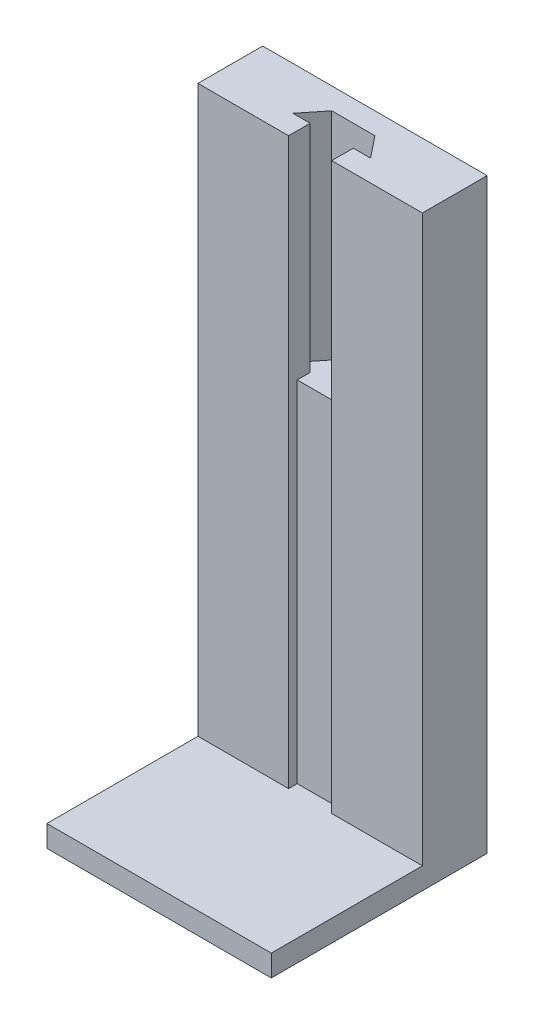
SolidWorks part; units mm, degrees
ref_plane "Front Plane" through (0, 0, 0) normal (0, 0, 1) x (1, 0, 0)
ref_plane "Top Plane" through (0, 0, 0) normal (0, 1, 0) x (1, 0, 0)
ref_plane "Right Plane" through (0, 0, 0) normal (1, 0, 0) x (0, 0, -1)
sketch "Sketch1" plane through (0, 0, 0) normal (0, 1, 0) x (1, 0, 0)
  line L1 (-26, -25) -> (26, -25)
  line L2 (-26, -25) -> (-26, 25)
  line L3 (-26, 25) -> (26, 25)
  line L4 (26, -25) -> (26, 25)
  line L5 (-26, -25) -> (26, 25) construction
  line L6 (-26, 25) -> (26, -25) construction
  point P0 (0, 0)
  dimension "D1" = 50
  dimension "D2" = 52
extrude "Boss-Extrude1" add sketch "Sketch1" along normal blind 5
sketch "Sketch2" plane through (0, 5, 0) normal (0, 1, 0) x (1, 0, 0)
  line L0 (26, -25) -> (26, 25) construction
  line L1 (-26, 25) -> (26, 25)
  line L2 (-26, 25) -> (-26, 10)
  line L3 (-26, 10) -> (26, 10)
  line L4 (26, 25) -> (26, 10)
  dimension "D1" = 15
extrude "Boss-Extrude2" add sketch "Sketch2" along normal blind 131
sketch "Sketch3" plane through (0, 136, 0) normal (0, 1, 0) x (1, 0, 0)
  line L0 (0, 25) -> (0, 10) construction
  line L1 (26, 25) -> (-26, 25) construction
  line L2 (-26, 10) -> (26, 10) construction
  line L3 (-5, 10) -> (5, 10)
  line L4 (-26, 10) -> (26, 10) construction
  line L5 (5, 10) -> (5, 15)
  line L6 (5, 15) -> (9, 15)
  line L7 (9, 15) -> (5, 20)
  line L8 (5, 20) -> (-5, 20)
  line L9 (-5, 20) -> (-9, 15)
  line L10 (-9, 15) -> (-5, 15)
  line L11 (-5, 15) -> (-5, 10)
  dimension "D1" = 10
  dimension "D2" = 5
  dimension "D3" = 5
  dimension "D4" = 4
extrude "Cut-Extrude1" cut sketch "Sketch3" against normal blind 50
sketch "Sketch4" plane through (0, 86, 0) normal (0, 1, 0) x (1, 0, 0)
  line L0 (-5, 10) -> (5, 10) construction
  line L1 (-5, 10) -> (5, 10)
  line L2 (-5, 10) -> (-5, 12)
  line L3 (-5, 12) -> (5, 12)
  line L4 (5, 10) -> (5, 12)
  line L5 (0, 20) -> (0, 10) construction
  line L6 (5, 20) -> (-5, 20) construction
  line L7 (-5, 15) -> (-5, 10) construction
  dimension "D1" = 2
extrude "Cut-Extrude2" cut sketch "Sketch4" against normal blind 81
